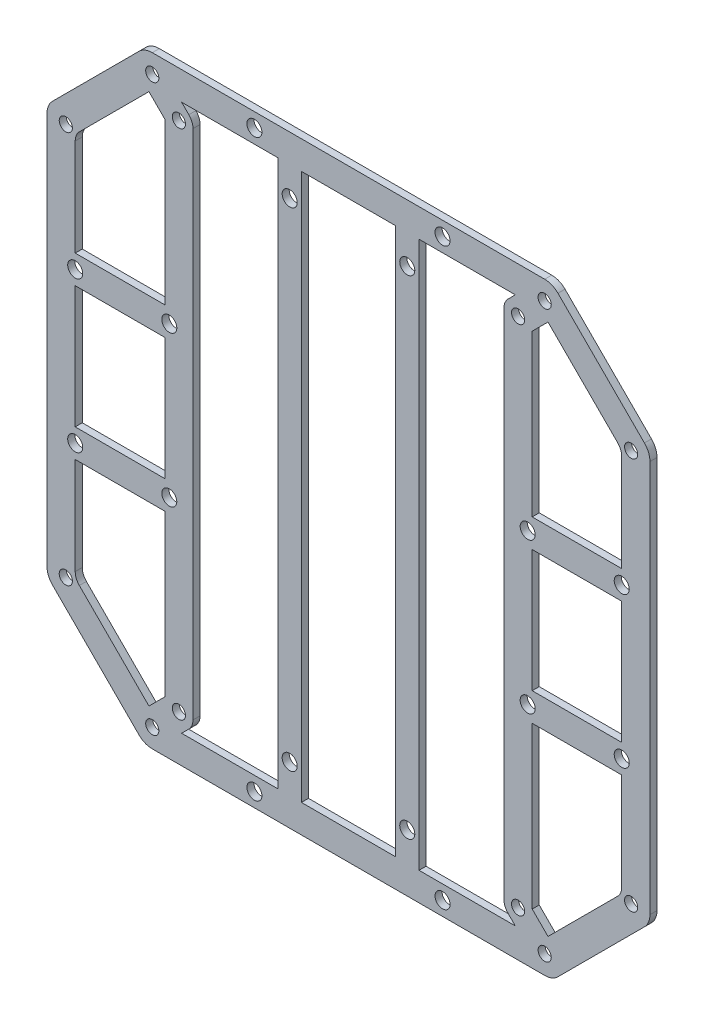
SolidWorks part; units mm, degrees
ref_plane "Front" through (0, 0, 0) normal (0, 0, 1) x (1, 0, 0)
ref_plane "Top" through (0, 0, 0) normal (0, 1, 0) x (1, 0, 0)
ref_plane "Right" through (0, 0, 0) normal (1, 0, 0) x (0, 0, -1)
sketch "Sketch1" plane through (0, 0, 0) normal (0, 0, 1) x (1, 0, 0)
  line L0 (-56.5685, 42.4264) -> (-49.621, 35.4789)
  line L4 (-35.8888, 73.4121) -> (-35.8888, 92.2659)
  line L9 (-42.4264, 56.5685) -> (-35.4789, 49.621)
  line L10 (-60.8112, 38.1838) -> (-74.9577, 24.0372)
  line L12 (-57.3374, 34.71) -> (-52.937, 30.3096)
  line L13 (-57.3374, 34.71) -> (-60.8112, 38.1838)
  line L14 (65.0538, 42.4264) -> (74.8359, 32.6443)
  line L16 (-41.8888, 80.4121) -> (-41.8888, 65.5914)
  line L17 (-35.8888, 67.4121) -> (-35.8888, 58.5162)
  line L19 (-41.8888, 80.4121) -> (-48.0398, 86.5631)
  line L27 (0, 67.4121) -> (-35.8888, 67.4121)
  line L28 (-53.7401, 53.7401) -> (-41.8888, 65.5914)
  line L41 (-35.8888, 58.5162) -> (-30.3096, 52.937)
  line L42 (-30.3096, 52.937) -> (-35.8888, 58.5162)
  line L45 (-53.7401, 53.7401) -> (-65.0538, 42.4264)
  line L46 (42.4264, 56.5685) -> (56.5685, 42.4264)
  line L64 (0, 0) -> (20.276, 0)
  line L74 (-84.8842, 42.6927) -> (-74.8359, 32.6443)
  line L77 (-86.0372, 35.3071) -> (-74.9577, 24.0372)
  line L79 (-42.4264, 56.5685) -> (-56.5685, 42.4264)
  line L82 (-65.0538, 42.4264) -> (-74.8359, 32.6443)
  line L86 (86.0372, 35.3071) -> (74.9577, 24.0372)
  line L87 (84.8842, 42.6927) -> (74.8359, 32.6443)
  line L90 (53.7401, 53.7401) -> (65.0538, 42.4264)
  line L91 (30.3096, 52.937) -> (35.8888, 58.5162)
  line L94 (-35.8888, 73.4121) -> (35.8888, 73.4121)
  line L95 (35.8888, 58.5162) -> (30.3096, 52.937)
  line L96 (53.7401, 53.7401) -> (41.8888, 65.5914)
  line L97 (41.8888, 80.4121) -> (41.8888, 65.5914)
  line L98 (0, 0) -> (0, 18.683)
  line L99 (35.8888, 67.4121) -> (35.8888, 58.5162)
  line L100 (41.8888, 80.4121) -> (48.0398, 86.5631)
  line L101 (57.3374, 34.71) -> (60.8112, 38.1838)
  line L102 (57.3374, 34.71) -> (52.937, 30.3096)
  line L103 (60.8112, 38.1838) -> (74.9577, 24.0372)
  line L109 (42.4264, 56.5685) -> (35.4789, 49.621)
  line L110 (35.8888, 73.4121) -> (35.8888, 92.2659)
  line L111 (56.5685, 42.4264) -> (49.621, 35.4789)
  line L112 (0, 67.4121) -> (35.8888, 67.4121)
  line L113 (0, -67.4121) -> (35.8888, -67.4121)
  line L114 (56.5685, -42.4264) -> (49.621, -35.4789)
  line L115 (35.8888, -73.4121) -> (35.8888, -92.2659)
  line L116 (42.4264, -56.5685) -> (35.4789, -49.621)
  line L117 (60.8112, -38.1838) -> (74.9577, -24.0372)
  line L118 (57.3374, -34.71) -> (52.937, -30.3096)
  line L119 (57.3374, -34.71) -> (60.8112, -38.1838)
  line L120 (41.8888, -80.4121) -> (48.0398, -86.5631)
  line L121 (35.8888, -67.4121) -> (35.8888, -58.5162)
  line L122 (0, 0) -> (0, -18.683)
  line L123 (41.8888, -80.4121) -> (41.8888, -65.5914)
  line L124 (53.7401, -53.7401) -> (41.8888, -65.5914)
  line L125 (35.8888, -58.5162) -> (30.3096, -52.937)
  line L126 (-35.8888, -73.4121) -> (35.8888, -73.4121)
  line L127 (30.3096, -52.937) -> (35.8888, -58.5162)
  line L128 (53.7401, -53.7401) -> (65.0538, -42.4264)
  line L129 (84.8842, -42.6927) -> (74.8359, -32.6443)
  line L130 (86.0372, -35.3071) -> (74.9577, -24.0372)
  line L131 (-65.0538, -42.4264) -> (-74.8359, -32.6443)
  line L132 (-42.4264, -56.5685) -> (-56.5685, -42.4264)
  line L133 (-86.0372, -35.3071) -> (-74.9577, -24.0372)
  line L134 (-84.8842, -42.6927) -> (-74.8359, -32.6443)
  line L135 (42.4264, -56.5685) -> (56.5685, -42.4264)
  line L136 (-53.7401, -53.7401) -> (-65.0538, -42.4264)
  line L137 (-30.3096, -52.937) -> (-35.8888, -58.5162)
  line L138 (-35.8888, -58.5162) -> (-30.3096, -52.937)
  line L139 (-53.7401, -53.7401) -> (-41.8888, -65.5914)
  line L140 (0, -67.4121) -> (-35.8888, -67.4121)
  line L142 (-41.8888, -80.4121) -> (-48.0398, -86.5631)
  line L143 (-35.8888, -67.4121) -> (-35.8888, -58.5162)
  line L144 (-41.8888, -80.4121) -> (-41.8888, -65.5914)
  line L145 (65.0538, -42.4264) -> (74.8359, -32.6443)
  line L146 (-57.3374, -34.71) -> (-60.8112, -38.1838)
  line L147 (-57.3374, -34.71) -> (-52.937, -30.3096)
  line L148 (-60.8112, -38.1838) -> (-74.9577, -24.0372)
  line L149 (-42.4264, -56.5685) -> (-35.4789, -49.621)
  line L150 (-35.8888, -73.4121) -> (-35.8888, -92.2659)
  line L151 (-56.5685, -42.4264) -> (-49.621, -35.4789)
  arc A22 (-35.8888, 92.2659) -> (-48.0398, 86.5631) centre (0, 0) ccw
  arc A23 (-84.8842, 42.6927) -> (-89.7245, 41.8392) centre (-87.0055, 40.5714) ccw
  circle A24 centre (-36.0624, 54.4472) radius 1.4
  circle A25 centre (-54.4472, 36.0624) radius 1.4
  circle A26 centre (-60.1041, 41.7193) radius 1.4
  circle A27 centre (-41.7193, 60.1041) radius 1.4
  arc A31 (-52.937, 30.3096) -> (-52.937, -30.3096) centre (0, 0) ccw
  arc A32 (-86.0372, 35.3071) -> (-83.3812, -41.1896) centre (0, 0) ccw
  arc A35 (-89.7245, 41.8392) -> (-89.7245, -41.8392) centre (0, 0) ccw
  circle A38 centre (41.3657, 41.3657) radius 1.6
  circle A40 centre (87.0055, 40.5714) radius 1.6
  circle A41 centre (41.7193, 60.1041) radius 1.4
  circle A42 centre (60.1041, 41.7193) radius 1.4
  circle A43 centre (54.4472, 36.0624) radius 1.4
  circle A45 centre (0, 0) radius 56
  circle A50 centre (36.0624, 54.4472) radius 1.4
  arc A53 (84.8842, 42.6927) -> (89.7245, 41.8392) centre (87.0055, 40.5714) cw
  arc A55 (35.8888, 92.2659) -> (48.0398, 86.5631) centre (0, 0) cw
  circle A57 centre (-87.0055, 40.5714) radius 1.6
  circle A58 centre (-87.0055, -40.5714) radius 1.6
  circle A59 centre (87.0055, -40.5714) radius 1.6
  circle A60 centre (87.0055, 40.5714) radius 1.6
  circle A61 centre (-40.5714, 87.0055) radius 1.6
  circle A63 centre (40.5714, -87.0055) radius 1.6
  circle A64 centre (-40.5714, -87.0055) radius 1.6
  circle A66 centre (41.3657, 41.3657) radius 1.6
  circle A67 centre (41.3657, -41.3657) radius 1.6
  circle A69 centre (-41.3657, 41.3657) radius 1.6
  circle A78 centre (-41.3657, -41.3657) radius 1.6 [skipped]
  circle A82 centre (40.5714, 87.0055) radius 1.6
  arc A83 (-35.4789, 49.621) -> (-49.621, 35.4789) centre (0, 0) ccw
  arc A84 (30.3096, 52.937) -> (-30.3096, 52.937) centre (0, 0) ccw
  arc A85 (49.621, 35.4789) -> (35.4789, 49.621) centre (0, 0) ccw
  arc A86 (49.621, -35.4789) -> (35.4789, -49.621) centre (0, 0) cw
  arc A87 (30.3096, -52.937) -> (-30.3096, -52.937) centre (0, 0) cw
  arc A88 (-35.4789, -49.621) -> (-49.621, -35.4789) centre (0, 0) cw
  circle A89 centre (40.5714, -87.0055) radius 1.6
  circle A90 centre (-41.3657, -41.3657) radius 1.6
  circle A91 centre (41.3657, -41.3657) radius 1.6
  circle A92 centre (-40.5714, -87.0055) radius 1.6
  circle A93 centre (87.0055, -40.5714) radius 1.6
  circle A94 centre (-87.0055, -40.5714) radius 1.6
  arc A95 (35.8888, -92.2659) -> (48.0398, -86.5631) centre (0, 0) ccw
  arc A96 (84.8842, -42.6927) -> (89.7245, -41.8392) centre (87.0055, -40.5714) ccw
  circle A97 centre (36.0624, -54.4472) radius 1.4
  circle A98 centre (54.4472, -36.0624) radius 1.4
  circle A99 centre (60.1041, -41.7193) radius 1.4
  circle A100 centre (41.7193, -60.1041) radius 1.4
  circle A101 centre (87.0055, -40.5714) radius 1.6
  circle A102 centre (41.3657, -41.3657) radius 1.6
  circle A103 centre (-41.7193, -60.1041) radius 1.4
  circle A104 centre (-60.1041, -41.7193) radius 1.4
  circle A105 centre (-54.4472, -36.0624) radius 1.4
  circle A106 centre (-36.0624, -54.4472) radius 1.4
  arc A107 (-84.8842, -42.6927) -> (-89.7245, -41.8392) centre (-87.0055, -40.5714) cw
  arc A108 (-35.8888, -92.2659) -> (-48.0398, -86.5631) centre (0, 0) cw
  arc A109 (35.8888, -92.2659) -> (48.0398, -86.5631) centre (0, 0) ccw
  arc A110 (-49.621, -35.4789) -> (-35.4789, -49.621) centre (0, 0) ccw
  arc A111 (-48.0398, -86.5631) -> (-35.8888, -92.2659) centre (0, 0) ccw
  arc A112 (-30.3096, -52.937) -> (30.3096, -52.937) centre (0, 0) ccw
  arc A113 (89.7245, -41.8392) -> (89.7245, 41.8392) centre (0, 0) ccw
  arc A114 (83.3812, -41.1896) -> (86.0372, 35.3071) centre (0, 0) ccw
  arc A115 (35.4789, -49.621) -> (49.621, -35.4789) centre (0, 0) ccw
  arc A116 (52.937, -30.3096) -> (52.937, 30.3096) centre (0, 0) ccw
  dimension "D3" = 4
extrude "Boss-Extrude13" add sketch "Sketch1" along normal blind 1.5
fillet "Fillet2" radius 2 8 edges at (35.8888, 92.2659, 0.75) (48.0398, 86.5631, 0.75) (-35.8888, 92.2659, 0.75) (-48.0398, 86.5631, 0.75) (-48.0398, -86.5631, 0.75) (-35.8888, -92.2659, 0.75) (35.8888, -92.2659, 0.75) (48.0398, -86.5631, 0.75)
sketch "Sketch2" plane through (0, 0, 1.5) normal (0, 0, 1) x (1, 0, 0)
  line L0 (-41.7193, 64.1041) -> (41.7193, 64.1041)
  line L1 (-64.1041, 41.7193) -> (-64.1041, -41.7193)
  line L2 (-41.7193, -64.1041) -> (41.7193, -64.1041)
  line L3 (64.1041, 41.7193) -> (64.1041, -41.7193)
  line L4 (-62.9325, 44.5477) -> (-44.5477, 62.9325)
  line L5 (44.5477, 62.9325) -> (62.9325, 44.5477)
  line L7 (44.5477, -62.9325) -> (62.9325, -44.5477)
  line L9 (-62.9325, -44.5477) -> (-44.5477, -62.9325)
  arc A0 (-41.7193, 64.1041) -> (-44.5477, 62.9325) centre (-41.7193, 60.1041) ccw
  arc A1 (44.5477, 62.9325) -> (41.7193, 64.1041) centre (41.7193, 60.1041) ccw
  arc A2 (-62.9325, 44.5477) -> (-64.1041, 41.7193) centre (-60.1041, 41.7193) ccw
  arc A3 (64.1041, 41.7193) -> (62.9325, 44.5477) centre (60.1041, 41.7193) ccw
  arc A4 (62.9325, -44.5477) -> (64.1041, -41.7193) centre (60.1041, -41.7193) ccw
  arc A5 (41.7193, -64.1041) -> (44.5477, -62.9325) centre (41.7193, -60.1041) ccw
  arc A6 (-64.1041, -41.7193) -> (-62.9325, -44.5477) centre (-60.1041, -41.7193) ccw
  arc A7 (-44.5477, -62.9325) -> (-41.7193, -64.1041) centre (-41.7193, -60.1041) ccw
  circle A8 centre (0, 0) radius 149.802
extrude "Cut-Extrude1" cut sketch "Sketch2" against normal blind 10
sketch "Sketch3" plane through (0, 0, 1.5) normal (0, 0, 1) x (1, 0, 0)
  line L0 (-56.1041, -41.7193) -> (-56.1041, 41.7193)
  line L2 (-64.1041, 41.7193) -> (-64.1041, -41.7193)
  line L3 (-41.7193, -64.1041) -> (41.7193, -64.1041)
  line L5 (41.7193, -56.1041) -> (-41.7193, -56.1041)
  line L6 (56.1041, 41.7193) -> (56.1041, -41.7193)
  line L8 (64.1041, -41.7193) -> (64.1041, 41.7193)
  line L9 (-41.7193, 64.1041) -> (41.7193, 64.1041)
  line L11 (41.7193, 56.1041) -> (-41.7193, 56.1041)
  arc A0 (-64.1041, 41.7193) -> (-56.1041, 41.7193) centre (-60.1041, 41.7193) ccw
  arc A1 (-41.7193, 56.1041) -> (-41.7193, 64.1041) centre (-41.7193, 60.1041) ccw
  arc A2 (41.7193, 64.1041) -> (41.7193, 56.1041) centre (41.7193, 60.1041) ccw
  arc A3 (56.1041, 41.7193) -> (64.1041, 41.7193) centre (60.1041, 41.7193) ccw
  arc A4 (64.1041, -41.7193) -> (56.1041, -41.7193) centre (60.1041, -41.7193) ccw
  arc A5 (41.7193, -56.1041) -> (41.7193, -64.1041) centre (41.7193, -60.1041) ccw
  arc A6 (-41.7193, -64.1041) -> (-41.7193, -56.1041) centre (-41.7193, -60.1041) ccw
  arc A7 (-56.1041, -41.7193) -> (-64.1041, -41.7193) centre (-60.1041, -41.7193) ccw
extrude "Boss-Extrude14" add sketch "Sketch3" against normal up to surface (1.5 mm away) up to face at (-34.6624, -54.4472, 0)
sketch "Sketch4" plane through (0, 0, 0) normal (0, 0, -1) x (-1, 0, 0)
  line L2 (-18.5719, 58.1041) -> (-35.4767, 58.1041)
  line L3 (-30.3096, 52.937) -> (-35.4767, 58.1041)
  line L4 (0, 16.1613) -> (0, 18.1264)
  line L5 (30.3096, 52.937) -> (35.4767, 58.1041)
  line L6 (18.5719, 58.1041) -> (35.4767, 58.1041)
  line L7 (-41.3657, 41.3657) -> (-46.6028, 46.6028)
  line L8 (-58.1041, -18.5719) -> (-58.1041, -35.4767)
  line L9 (-52.937, -30.3096) -> (-58.1041, -35.4767)
  line L10 (-52.937, 30.3096) -> (-58.1041, 35.4767)
  line L11 (-58.1041, 18.5719) -> (-58.1041, 35.4767)
  line L13 (18.5719, -58.1041) -> (35.4767, -58.1041)
  line L14 (30.3096, -52.937) -> (35.4767, -58.1041)
  line L15 (-30.3096, -52.937) -> (-35.4767, -58.1041)
  line L16 (-18.5719, -58.1041) -> (-35.4767, -58.1041)
  line L17 (41.3657, -41.3657) -> (46.6028, -46.6028)
  line L18 (58.1041, 18.5719) -> (58.1041, 35.4767)
  line L19 (52.937, 30.3096) -> (58.1041, 35.4767)
  line L21 (52.937, -30.3096) -> (58.1041, -35.4767)
  line L22 (58.1041, -18.5719) -> (58.1041, -35.4767)
  arc A0 (-18.5719, 58.1041) -> (-30.3096, 52.937) centre (0, 0) ccw
  arc A1 (18.5719, 58.1041) -> (30.3096, 52.937) centre (0, 0) cw
  arc A2 (-58.1041, -18.5719) -> (-52.937, -30.3096) centre (0, 0) ccw
  arc A3 (-58.1041, 18.5719) -> (-52.937, 30.3096) centre (0, 0) cw
  arc A4 (18.5719, -58.1041) -> (30.3096, -52.937) centre (0, 0) ccw
  arc A5 (-18.5719, -58.1041) -> (-30.3096, -52.937) centre (0, 0) cw
  arc A6 (58.1041, 18.5719) -> (52.937, 30.3096) centre (0, 0) ccw
  arc A7 (58.1041, -18.5719) -> (52.937, -30.3096) centre (0, 0) cw
extrude "Cut-Extrude2" cut sketch "Sketch4" against normal blind 10 contours A2 L8 L9 | L16 A5 L15 | A4 L13 L14 | L22 A7 L21 | A6 L18 L19 | A0 L2 L3 | L11 L10 A3 | L6 L5 A1
sketch "Sketch5" plane through (0, 0, 0) normal (0, 0, -1) x (-1, 0, 0)
  circle A0 centre (-22, 58.1041) radius 1.6
  circle A1 centre (22, 58.1041) radius 1.6
  circle A2 centre (22, -58.1041) radius 1.6
  circle A3 centre (-22, -58.1041) radius 1.6
extrude "Cut-Extrude4" cut sketch "Sketch5" against normal blind 10
sketch "Sketch6" plane through (0, 0, 0) normal (0, 0, -1) x (-1, 0, 0)
  circle A0 centre (0, 0) radius 61
extrude "Cut-Extrude5" cut sketch "Sketch6" against normal blind 10
sketch "Sketch7" plane through (0, 0, 1.5) normal (0, 0, 1) x (1, 0, 0)
  line L0 (-58.1041, 18.5719) -> (-58.1041, -18.5719)
  line L1 (-58.1041, -18.5719) -> (-62.4246, -11.3355)
  line L2 (-62.4246, -11.3355) -> (-62.4246, 6.6343)
  line L3 (-62.4246, 6.6343) -> (-58.1041, 18.5719)
  line L4 (-18.5719, 58.1041) -> (18.5719, 58.1041)
  line L5 (18.5719, 58.1041) -> (11.1047, 62.1939)
  line L6 (11.1047, 62.1939) -> (-9.9823, 62.1939)
  line L7 (-9.9823, 62.1939) -> (-18.5719, 58.1041)
  line L8 (58.1041, 18.5719) -> (58.1041, -18.5719)
  line L9 (58.1041, -18.5719) -> (62.0675, -11.3355)
  line L10 (62.0675, -11.3355) -> (62.0675, 12.6031)
  line L11 (62.0675, 12.6031) -> (58.1041, 18.5719)
  line L12 (-18.5719, -58.1041) -> (18.5719, -58.1041)
  line L13 (18.5719, -58.1041) -> (9.2716, -62.5322)
  line L14 (9.2716, -62.5322) -> (-14.2771, -62.5322)
  line L15 (-14.2771, -62.5322) -> (-18.5719, -58.1041)
extrude "Boss-Extrude15" add sketch "Sketch7" against normal up to surface (1.5 mm away) up to face at (0, 0, 0)
sketch "Sketch8" plane through (0, 0, 1.5) normal (0, 0, 1) x (1, 0, 0)
  line L1 (-58.1041, -35.4767) -> (-58.1041, 35.4767) construction
  circle A0 centre (-58.1041, 16) radius 1.6
  circle A1 centre (-58.1041, -16) radius 1.6
  circle A2 centre (58.1041, -16) radius 1.6
  circle A3 centre (58.1041, 16) radius 1.6
extrude "Cut-Extrude6" cut sketch "Sketch8" against normal blind 10
sketch "Sketch9" plane through (0, 0, 1.5) normal (0, 0, 1) x (1, 0, 0)
  line L0 (-23.6, -58.1041) -> (-20.4, -58.1041)
  line L1 (23.6, 58.1041) -> (20.4, 58.1041)
  line L2 (-20.4, 58.1041) -> (-23.6, 58.1041)
  line L3 (20.4, -58.1041) -> (23.6, -58.1041)
  arc A0 (-20.4, 58.1041) -> (-23.6, 58.1041) centre (-22, 58.1041) ccw
  arc A1 (23.6, 58.1041) -> (20.4, 58.1041) centre (22, 58.1041) ccw
  arc A2 (-23.6, -58.1041) -> (-20.4, -58.1041) centre (-22, -58.1041) ccw
  arc A3 (20.4, -58.1041) -> (23.6, -58.1041) centre (22, -58.1041) ccw
extrude "Boss-Extrude16" add sketch "Sketch9" against normal up to surface (1.5 mm away) up to face at (0, 0, 0)
sketch "Sketch10" plane through (0, 0, 1.5) normal (0, 0, 1) x (1, 0, 0)
  circle A0 centre (-61.8459, 37.7923) radius 1.83
  circle A1 centre (-60.9692, -37.3357) radius 1.4801
  circle A2 centre (60.7188, -37.3357) radius 1.1535
  circle A3 centre (60.2848, 38.1877) radius 1.1387
extrude "Boss-Extrude17" add sketch "Sketch10" against normal up to surface (1.5 mm away) up to face at (0, 0, 0)
sketch "Sketch11" plane through (0, 0, 1.5) normal (0, 0, 1) x (1, 0, 0)
  line L2 (-40.936, 47.9271) -> (-30.6833, 44.5727)
  line L3 (-30.6833, 44.5727) -> (-23.2572, 49.487)
  line L4 (-23.2572, 49.487) -> (-23.2572, 53.3868)
  line L6 (-33.9411, 56.5685) -> (-23.2572, 53.3868)
  line L7 (-38.1838, 52.3259) -> (-40.936, 47.9271)
  line L10 (-52.3259, 38.1838) -> (-47.9271, 40.936)
  line L11 (-56.5685, 33.9411) -> (-53.3868, 23.2572)
  line L13 (-49.487, 23.2572) -> (-53.3868, 23.2572)
  line L14 (-44.5727, 30.6833) -> (-49.487, 23.2572)
  line L15 (-47.9271, 40.936) -> (-44.5727, 30.6833)
  line L17 (47.9271, 40.936) -> (44.5727, 30.6833)
  line L18 (44.5727, 30.6833) -> (49.487, 23.2572)
  line L19 (49.487, 23.2572) -> (53.3868, 23.2572)
  line L20 (56.5685, 33.9411) -> (53.3868, 23.2572)
  line L21 (52.3259, 38.1838) -> (47.9271, 40.936)
  line L22 (38.1838, 52.3259) -> (40.936, 47.9271)
  line L23 (33.9411, 56.5685) -> (23.2572, 53.3868)
  line L24 (23.2572, 49.487) -> (23.2572, 53.3868)
  line L25 (30.6833, 44.5727) -> (23.2572, 49.487)
  line L26 (40.936, 47.9271) -> (30.6833, 44.5727)
  line L28 (40.936, -47.9271) -> (30.6833, -44.5727)
  line L29 (30.6833, -44.5727) -> (23.2572, -49.487)
  line L30 (23.2572, -49.487) -> (23.2572, -53.3868)
  line L31 (33.9411, -56.5685) -> (23.2572, -53.3868)
  line L32 (38.1838, -52.3259) -> (40.936, -47.9271)
  line L33 (52.3259, -38.1838) -> (47.9271, -40.936)
  line L34 (56.5685, -33.9411) -> (53.3868, -23.2572)
  line L35 (49.487, -23.2572) -> (53.3868, -23.2572)
  line L36 (44.5727, -30.6833) -> (49.487, -23.2572)
  line L37 (47.9271, -40.936) -> (44.5727, -30.6833)
  line L38 (-47.9271, -40.936) -> (-44.5727, -30.6833)
  line L39 (-44.5727, -30.6833) -> (-49.487, -23.2572)
  line L40 (-49.487, -23.2572) -> (-53.3868, -23.2572)
  line L41 (-56.5685, -33.9411) -> (-53.3868, -23.2572)
  line L42 (-52.3259, -38.1838) -> (-47.9271, -40.936)
  line L43 (-38.1838, -52.3259) -> (-40.936, -47.9271)
  line L44 (-33.9411, -56.5685) -> (-23.2572, -53.3868)
  line L45 (-23.2572, -49.487) -> (-23.2572, -53.3868)
  line L46 (-30.6833, -44.5727) -> (-23.2572, -49.487)
  line L47 (-40.936, -47.9271) -> (-30.6833, -44.5727)
  arc A0 (-56.5685, 33.9411) -> (-52.3259, 38.1838) centre (-54.4472, 36.0624) ccw
  arc A1 (-38.1838, 52.3259) -> (-33.9411, 56.5685) centre (-36.0624, 54.4472) ccw
  arc A2 (-52.3259, 38.1838) -> (-56.5685, 33.9411) centre (-54.4472, 36.0624) cw
  arc A3 (52.3259, 38.1838) -> (56.5685, 33.9411) centre (54.4472, 36.0624) ccw
  arc A4 (38.1838, 52.3259) -> (33.9411, 56.5685) centre (36.0624, 54.4472) cw
  arc A5 (56.5685, 33.9411) -> (52.3259, 38.1838) centre (54.4472, 36.0624) cw
  arc A6 (56.5685, -33.9411) -> (52.3259, -38.1838) centre (54.4472, -36.0624) ccw
  arc A7 (38.1838, -52.3259) -> (33.9411, -56.5685) centre (36.0624, -54.4472) ccw
  arc A8 (52.3259, -38.1838) -> (56.5685, -33.9411) centre (54.4472, -36.0624) cw
  arc A9 (-52.3259, -38.1838) -> (-56.5685, -33.9411) centre (-54.4472, -36.0624) ccw
  arc A10 (-38.1838, -52.3259) -> (-33.9411, -56.5685) centre (-36.0624, -54.4472) cw
  arc A11 (-56.5685, -33.9411) -> (-52.3259, -38.1838) centre (-54.4472, -36.0624) cw
extrude "Cut-Extrude7" cut sketch "Sketch11" against normal blind 10 contours A9 L42 L38 L39 L40 L41 | L43 A10 L44 L45 L46 L47 | A7 L32 L28 L29 L30 L31 | A6 L34 L35 L36 L37 L33 | A3 L21 L17 L18 L19 L20 | L22 A4 L23 L24 L25 L26 | A1 L7 L2 L3 L4 L6 | A0 L11 L13 L14 L15 L10
sketch "Sketch12" plane through (0, 0, 0) normal (0, 0, -1) x (-1, 0, 0)
  line L2 (-33.0624, -54.4472) -> (-33.0624, 54.4472)
  line L4 (-39.0624, 0) -> (-39.0624, 53.2046)
  line L5 (-42.4264, 56.5685) -> (-38.1838, 52.3259) construction
  line L6 (-39.0624, 53.2046) -> (-36.0624, 52.5116)
  line L7 (-36.0624, 52.5116) -> (-33.0624, 54.4472)
  line L8 (-39.0624, 0) -> (-39.0624, -54.4472)
  line L9 (-39.0624, -54.4472) -> (-36.0624, -52.5116)
  line L10 (-36.0624, -52.5116) -> (-33.0624, -54.4472)
  line L11 (36.0624, -52.5116) -> (33.0624, -54.4472)
  line L12 (39.0624, -54.4472) -> (36.0624, -52.5116)
  line L13 (39.0624, 0) -> (39.0624, -54.4472)
  line L14 (36.0624, 52.5116) -> (33.0624, 54.4472)
  line L15 (39.0624, 53.2046) -> (36.0624, 52.5116)
  line L16 (39.0624, 0) -> (39.0624, 53.2046)
  line L18 (33.0624, -54.4472) -> (33.0624, 54.4472)
  arc A0 (-33.9411, -56.5685) -> (-38.1838, -52.3259) centre (-36.0624, -54.4472) ccw construction
  arc A1 (-38.1838, 52.3259) -> (-33.9411, 56.5685) centre (-36.0624, 54.4472) ccw construction
extrude "Boss-Extrude18" add sketch "Sketch12" against normal up to surface (1.5 mm away) up to face at (0, 0, 1.5)
sketch "Sketch13" plane through (0, 0, 1.5) normal (0, 0, 1) x (1, 0, 0)
  line L1 (-58.1041, 19) -> (-38.1041, 19)
  line L2 (-58.1041, 13) -> (-38.1041, 13)
  line L3 (-58.1041, -13) -> (-38.1041, -13)
  line L4 (-58.1041, -19) -> (-38.1041, -19)
  line L6 (58.1041, -19) -> (38.1041, -19)
  line L7 (58.1041, -13) -> (38.1041, -13)
  line L8 (58.1041, 13) -> (38.1041, 13)
  line L9 (58.1041, 19) -> (38.1041, 19)
  circle A0 centre (-58.1041, 16) radius 1.6
  circle A1 centre (-38.1041, 16) radius 1.6
  arc A2 (-38.1041, 13) -> (-38.1041, 19) centre (-38.1041, 16) ccw
  arc A3 (-58.1041, 19) -> (-58.1041, 13) centre (-58.1041, 16) ccw
  arc A4 (-58.1041, -19) -> (-58.1041, -13) centre (-58.1041, -16) cw
  arc A5 (-38.1041, -13) -> (-38.1041, -19) centre (-38.1041, -16) cw
  circle A6 centre (-38.1041, -16) radius 1.6
  circle A7 centre (-58.1041, -16) radius 1.6
  circle A8 centre (58.1041, -16) radius 1.6
  circle A9 centre (38.1041, -16) radius 1.6
  arc A10 (38.1041, -13) -> (38.1041, -19) centre (38.1041, -16) ccw
  arc A11 (58.1041, -19) -> (58.1041, -13) centre (58.1041, -16) ccw
  arc A12 (58.1041, 19) -> (58.1041, 13) centre (58.1041, 16) cw
  arc A13 (38.1041, 13) -> (38.1041, 19) centre (38.1041, 16) cw
  circle A14 centre (38.1041, 16) radius 1.6
  circle A15 centre (58.1041, 16) radius 1.6
extrude "Boss-Extrude19" add sketch "Sketch13" against normal up to surface (1.5 mm away) up to face at (-52.5928, 0, 0)
sketch "Sketch14" plane through (0, 0, 1.5) normal (0, 0, 1) x (1, 0, 0)
  circle A0 centre (-38.1041, 16) radius 1.6
  circle A1 centre (-38.1041, -16) radius 1.6
  circle A2 centre (38.1041, 16) radius 1.6
  circle A3 centre (38.1041, -16) radius 1.6
extrude "Cut-Extrude8" cut sketch "Sketch14" against normal blind 10
sketch "Sketch15" plane through (0, 0, 1.5) normal (0, 0, 1) x (1, 0, 0)
  line L0 (-58.1041, 35.4767) -> (-58.1041, 40.8909)
  line L1 (-56.5685, 42.4264) -> (-58.1041, 40.8909)
  line L2 (-56.5685, 42.4264) -> (-46.2133, 41.0593)
  line L3 (-46.2133, 41.0593) -> (-49.5225, 25.6624)
  line L4 (-49.5225, 25.6624) -> (-58.1041, 35.4767)
  line L6 (-49.5225, -25.6624) -> (-58.1041, -35.4767)
  line L7 (-46.2133, -41.0593) -> (-49.5225, -25.6624)
  line L8 (-56.5685, -42.4264) -> (-46.2133, -41.0593)
  line L9 (-56.5685, -42.4264) -> (-58.1041, -40.8909)
  line L10 (-58.1041, -35.4767) -> (-58.1041, -40.8909)
  line L12 (58.1041, -35.4767) -> (58.1041, -40.8909)
  line L13 (56.5685, -42.4264) -> (58.1041, -40.8909)
  line L14 (56.5685, -42.4264) -> (46.2133, -41.0593)
  line L15 (46.2133, -41.0593) -> (49.5225, -25.6624)
  line L16 (49.5225, -25.6624) -> (58.1041, -35.4767)
  line L17 (49.5225, 25.6624) -> (58.1041, 35.4767)
  line L18 (46.2133, 41.0593) -> (49.5225, 25.6624)
  line L19 (56.5685, 42.4264) -> (46.2133, 41.0593)
  line L20 (56.5685, 42.4264) -> (58.1041, 40.8909)
  line L21 (58.1041, 35.4767) -> (58.1041, 40.8909)
extrude "Cut-Extrude9" cut sketch "Sketch15" against normal blind 10
fillet "Fillet3" radius 3 4 edges at (58.1041, 40.8909, 0.75) (58.1041, -40.8909, 0.75) (-58.1041, -40.8909, 0.75) (-58.1041, 40.8909, 0.75)
sketch "Sketch16" plane through (0, 0, 1.5) normal (0, 0, 1) x (1, 0, 0)
  line L1 (35.4767, 58.1041) -> (-35.4767, 58.1041) construction
  line L2 (10, 58.1041) -> (15, 58.1041)
  line L3 (15, 58.1041) -> (15, -58.1041)
  line L4 (35.4767, -58.1041) -> (-35.4767, -58.1041) construction
  line L5 (15, -58.1041) -> (10, -58.1041)
  line L6 (10, -58.1041) -> (10, 58.1041)
  line L7 (0, 0) -> (0, 12.8452)
  line L8 (-10, -58.1041) -> (-10, 58.1041)
  line L9 (-15, -58.1041) -> (-10, -58.1041)
  line L10 (-15, 58.1041) -> (-15, -58.1041)
  line L11 (-10, 58.1041) -> (-15, 58.1041)
extrude "Boss-Extrude20" add sketch "Sketch16" against normal blind 1.5 contours L6 L5 L3 L2 | L8 L11 L10 L9
sketch "Sketch17" plane through (0, 0, 1.5) normal (0, 0, 1) x (1, 0, 0)
  circle A0 centre (12.5, -51.8959) radius 1.6
  circle A1 centre (-12.5, -51.8959) radius 1.6
  circle A2 centre (-12.5, 51.8959) radius 1.6
  circle A3 centre (12.5, 51.8959) radius 1.6
extrude "Cut-Extrude10" cut sketch "Sketch17" against normal blind 1.5
sketch "Sketch18" plane through (0, 0, 1.5) normal (0, 0, 1) x (1, 0, 0)
  line L0 (0, 0) -> (0, 61.1041)
  line L3 (0, 61.1041) -> (-20, 61.1041)
  line L4 (-20, 61.1041) -> (20, 61.1041)
  line L5 (0, 0) -> (0, -61.1041)
  line L6 (0, -61.1041) -> (20, -61.1041)
  line L7 (20, -61.1041) -> (0, -61.1041)
  line L8 (-18.4, -61.1041) -> (-20, -61.1041)
  line L9 (0, -61.1041) -> (-20, -61.1041)
  circle A0 centre (20, 61.1041) radius 1.6
  circle A1 centre (-20, 61.1041) radius 1.6
  circle A2 centre (-20, -61.1041) radius 1.6
  circle A3 centre (20, -61.1041) radius 1.6
extrude "Cut-Extrude12" cut sketch "Sketch18" against normal blind 4
